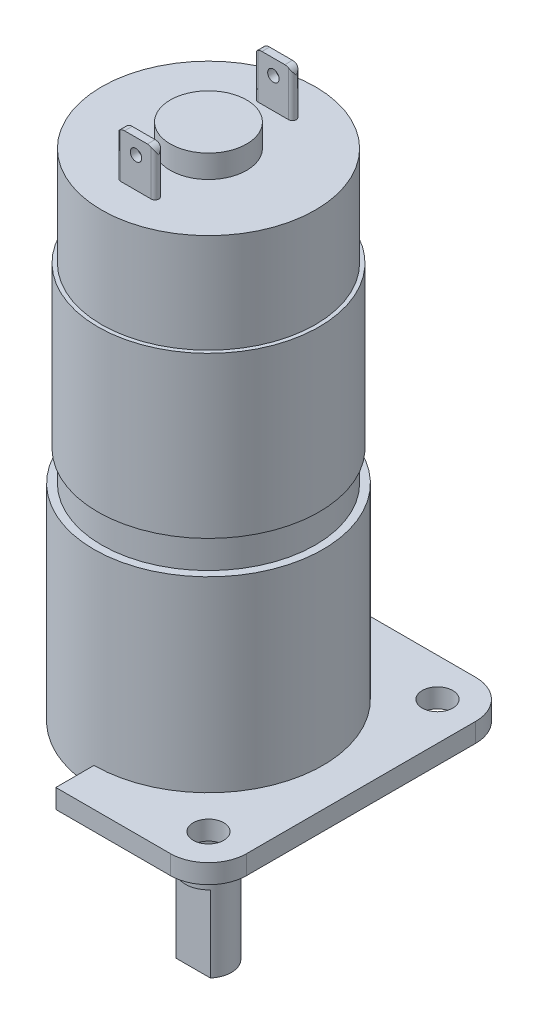
SolidWorks part; units mm, degrees
ref_plane "Alzado" through (0, 0, 0) normal (0, 0, 1) x (1, 0, 0)
ref_plane "Planta" through (0, 0, 0) normal (0, 1, 0) x (1, 0, 0)
ref_plane "Vista lateral" through (0, 0, 0) normal (1, 0, 0) x (0, 0, -1)
sketch "Croquis1" plane through (0, 0, 0) normal (0, 1, 0) x (1, 0, 0)
  circle A0 centre (0, 0) radius 14
  dimension "D1" = 28
extrude "Motor" add sketch "Croquis1" along normal blind 38
sketch "Croquis2" plane through (0, 38, 0) normal (0, 1, 0) x (1, 0, 0)
  circle A0 centre (0, 0) radius 5
  dimension "D1" = 10
extrude "Saliente posterior" add sketch "Croquis2" along normal blind 3
sketch "Croquis3" plane through (0, 38, 0) normal (0, 1, 0) x (1, 0, 0)
  line L0 (-10.7238, 9) -> (10.7238, 9) construction
  line L1 (-2, 9) -> (2, 9) construction
  line L2 (-2, 9.5) -> (2, 9.5)
  line L3 (-2, 8.5) -> (2, 8.5)
  line L4 (-14, 0) -> (14, 0) construction
  line L5 (-2, -9) -> (2, -9) construction
  line L6 (-2, -9.5) -> (2, -9.5)
  line L7 (-2, -8.5) -> (2, -8.5)
  circle A0 centre (0, 0) radius 14 construction
  arc A1 (-2, 9.5) -> (-2, 8.5) centre (-2, 9) ccw
  arc A2 (2, 8.5) -> (2, 9.5) centre (2, 9) ccw
  arc A3 (-2, -9.5) -> (-2, -8.5) centre (-2, -9) cw
  arc A4 (2, -8.5) -> (2, -9.5) centre (2, -9) cw
  point P7 (0, 9)
  point P17 (0, -9)
  dimension "D3" = 0.5
  dimension "D1" = 9
  dimension "D2" = 4
extrude "Bornes" add sketch "Croquis3" along normal blind 6
sketch "Croquis4" plane through (0, 0, 9.5) normal (0, 0, 1) x (1, 0, 0)
  line L0 (0, 44) -> (0, 38) construction
  line L1 (-2, 44) -> (2, 44) construction
  line L2 (-2, 38) -> (2, 38) construction
  line L3 (-2.5, 43) -> (2.5, 43) construction
  line L4 (-2.5, 44) -> (-2.5, 38) construction
  line L5 (2.5, 38) -> (2.5, 44) construction
  line L6 (-1.5, 44) -> (-1.5, 38) construction
  line L7 (14, 38) -> (-14, 38) construction
  line L8 (-2, 44) -> (-2.5, 44) construction
  line L9 (2.5, 43) -> (2.5, 44)
  line L10 (2.5, 44) -> (1.5, 44)
  line L11 (-2.5, 43) -> (-2.5, 44)
  line L12 (-2.5, 44) -> (-1.5, 44)
  arc A0 (-2.5, 43) -> (-1.5, 44) centre (-1.5, 43) cw
  arc A1 (2.5, 43) -> (1.5, 44) centre (1.5, 43) ccw
  circle A2 centre (0, 42) radius 0.75
  line M2 (2, 38) -> (2, 44)
  line M3 (2, 44) -> (-2, 44)
  line M4 (-2, 44) -> (-2, 38)
  dimension "D3" = 1.5
  dimension "D1" = 1
  dimension "D2" = 1
  dimension "D4" = 2
extrude "Agujero Bornes" cut sketch "Croquis4" against normal through all contours A2 | A1 L9 L10 M2 | A1 M2 M3 | L11 A0 L12 M4 | A0 M4 M3
sketch "Croquis5" plane through (0, 0, 0) normal (0, -1, 0) x (1, 0, 0)
  circle A0 centre (0, 0) radius 15
  dimension "D1" = 30
extrude "Caja reductora" add sketch "Croquis5" along normal blind 24.5
sketch "Croquis6" plane through (0, -24.5, 0) normal (0, -1, 0) x (1, 0, 0)
  line L1 (-15, 20) -> (15, 20)
  line L2 (-20, 15) -> (-20, -15)
  line L3 (-15, -20) -> (15, -20)
  line L4 (20, 15) -> (20, -15)
  line L5 (-20, 20) -> (20, -20) construction
  line L6 (-20, -20) -> (20, 20) construction
  circle A0 centre (-15, 15) radius 2
  circle A1 centre (15, 15) radius 2
  circle A2 centre (15, -15) radius 2
  circle A3 centre (-15, -15) radius 2
  arc A4 (-20, -15) -> (-15, -20) centre (-15, -15) ccw
  arc A5 (15, -20) -> (20, -15) centre (15, -15) ccw
  arc A6 (15, 20) -> (20, 15) centre (15, 15) cw
  arc A7 (-15, 20) -> (-20, 15) centre (-15, 15) ccw
  point P0 (0, 0)
  point P17 (0, 0)
  dimension "D3" = 4
  dimension "D6" = 5
  dimension "D1" = 40
  dimension "D2" = 40
  dimension "D4" = 5
  dimension "D5" = 4
extrude "Brida" add sketch "Croquis6" along normal blind 2.5
sketch "Croquis7" plane through (0, -27, 0) normal (0, -1, 0) x (1, 0, 0)
  circle A0 centre (0, 0) radius 6.5
  dimension "D1" = 13
extrude "Saliente eje" add sketch "Croquis7" along normal blind 13.5
sketch "Croquis8" plane through (0, -40.5, 0) normal (0, -1, 0) x (1, 0, 0)
  circle A0 centre (0, 0) radius 3
  dimension "D1" = 6
extrude "Eje" add sketch "Croquis8" along normal blind 13.5
sketch "Croquis9" plane through (0, -54, 0) normal (0, -1, 0) x (1, 0, 0)
  line L0 (-2.2361, 2) -> (2.2361, 2)
  circle A0 centre (0, 0) radius 3 construction
  circle A1 centre (0, 0) radius 3
  circle M1 centre (0, 0) radius 3
  dimension "D1" = 2
extrude "Corte Plano eje" cut sketch "Croquis9" against normal blind 10 contours L0 M1
sketch "Croquis10" plane through (0, -24.5, 0) normal (0, 1, 0) x (1, 0, 0)
  line L1 (-15, 20) -> (15, 20) construction
  line L2 (0, 20) -> (22.7102, 20)
  line L3 (0, 20) -> (0, -20.9832)
  line L4 (0, -20.9832) -> (22.7102, -20.9832)
  line L5 (22.7102, 20) -> (22.7102, -20.9832)
  circle A0 centre (0, 0) radius 15
  circle M2 centre (15, -15) radius 2
  line M4 (-20, 15) -> (-20, -15)
  arc M5 (-20, -15) -> (-15, -20) centre (-15, -15) ccw
  line M6 (-15, -20) -> (15, -20)
  arc M7 (15, -20) -> (20, -15) centre (15, -15) ccw
  line M8 (20, -15) -> (20, 15)
  circle M11 centre (-15, -15) radius 2
  circle M13 centre (0, 0) radius 15
extrude "Corte Brida" cut sketch "Croquis10" against normal blind 10 contours L2 M4 M5 M6 M7 M8 M13 M2 M11
sketch "Croquis11" plane through (0, 0, 0) normal (0, 1, 0) x (1, 0, 0)
  circle A0 centre (0, 0) radius 14.5
  dimension "D1" = 29
extrude "Saliente-Extruir1" add sketch "Croquis11" along normal blind 21 from offset 4
